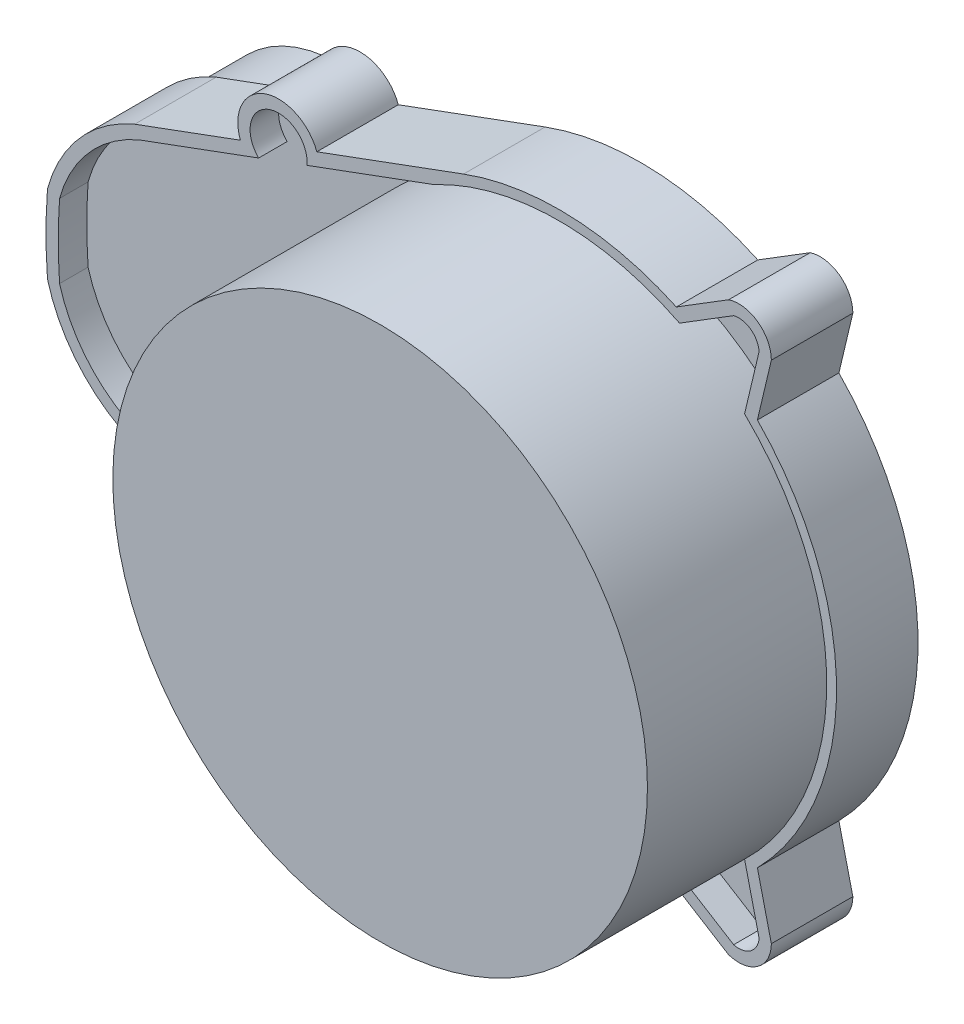
SolidWorks part; units mm, degrees
ref_plane "Plan de face" through (0, 0, 0) normal (0, 0, 1) x (1, 0, 0)
ref_plane "Plan de dessus" through (0, 0, 0) normal (0, 1, 0) x (1, 0, 0)
ref_plane "Plan de droite" through (0, 0, 0) normal (1, 0, 0) x (0, 0, -1)
sketch "Esquisse1" plane through (0, 0, 0) normal (0, 0, 1) x (1, 0, 0)
  line L0 (-11.7623, 31.9006) -> (-29.7675, 25.2618)
  line L1 (-52.1142, 17.0221) -> (-52.1142, -17.0221) construction
  line L2 (-45, 0) -> (0, 0) construction
  line L3 (-11.7623, 31.9006) -> (-11.7623, -31.9006) construction
  line L5 (-35, 25) -> (-34.4587, 23.532) construction
  line L6 (-39.15, 21.8022) -> (-52.1142, 17.0221)
  line L7 (-34.1447, 23.6478) -> (-34.7727, 23.4162)
  line L8 (20.756, 34.8016) -> (14.3413, 30.8274)
  line L9 (26, 31) -> (24.2884, 23.7923)
  line L10 (-63, 0) -> (35.5, 0) construction
  line L11 (55, 0) -> (-55, 0) construction
  line L12 (-35, -25) -> (-34.4587, -23.532) construction
  line L13 (26, -31) -> (24.2884, -23.7923)
  line L14 (20.756, -34.8016) -> (14.3413, -30.8274)
  line L15 (-34.1447, -23.6478) -> (-34.7727, -23.4162)
  line L16 (-39.15, -21.8022) -> (-52.1142, -17.0221)
  line L17 (-11.7623, -31.9006) -> (-29.7675, -25.2618)
  arc A1 (24.2884, -23.7923) -> (24.2884, 23.7923) centre (0, 0) ccw
  arc A3 (-62.8182, 4.7829) -> (-62.8182, -4.7829) centre (0, 0) ccw
  arc A4 (-52.1142, 17.0221) -> (-62.8182, 4.7829) centre (-45, 0) ccw
  circle A5 centre (22, 31) radius 1.6
  circle A6 centre (-35, 25) radius 1.6
  arc A7 (-29.7675, 25.2618) -> (-39.15, 21.8022) centre (-34.4587, 23.532) ccw
  arc A8 (26, 31) -> (20.756, 34.8016) centre (22, 31) ccw
  arc A9 (14.3413, 30.8274) -> (-11.7623, 31.9006) centre (0, 0) ccw
  arc A10 (14.3413, -30.8274) -> (-11.7623, -31.9006) centre (0, 0) cw
  arc A11 (26, -31) -> (20.756, -34.8016) centre (22, -31) cw
  arc A12 (-29.7675, -25.2618) -> (-39.15, -21.8022) centre (-34.4587, -23.532) cw
  circle A13 centre (-35, -25) radius 1.6
  circle A14 centre (22, -31) radius 1.6
  arc A15 (-52.1142, -17.0221) -> (-62.8182, -4.7829) centre (-45, 0) cw
  point P28 (-11.7623, 0)
  point P29 (-52.1142, 0)
  point P41 (34, 0)
  point P42 (-63, 0)
  dimension "D1" = 68
  dimension "D2" = 12
  dimension "D4" = 126
  dimension "D6" = 3.2
  dimension "D10" = 10
  dimension "D11" = 8
  dimension "D3" = 45
  dimension "D5" = 31
  dimension "D7" = 22
  dimension "D8" = 57
  dimension "D9" = 25
  dimension "D12" = 97
extrude "Boss.-Extru.1" add sketch "Esquisse1" along normal blind 10 contours A15 L16 A12 L17 A10 L14 A11 L13 A1 L9 A8 L8 A9 L0 A7 L6 A4 A3 A13 A5 A6 A14
sketch "Esquisse2" plane through (0, 0, 10) normal (0, 0, 1) x (1, 0, 0)
  circle A0 centre (0, 0) radius 32.8
  dimension "D1" = 65.6
extrude "Boss.-Extru.2" add sketch "Esquisse2" along normal blind 22
sketch "Esquisse3" plane through (0, 0, 10) normal (0, 0, 1) x (1, 0, 0)
  line L16 (-51.5646, -15.626) -> (-36.9068, -21.0306)
  line L17 (14.4327, -29.1195) -> (21.3751, -33.4206)
  line L18 (24.4952, -31.1553) -> (22.635, -23.3218)
  line L19 (22.635, 23.3218) -> (24.4952, 31.1553)
  line L20 (21.3751, 33.4206) -> (14.4327, 29.1195)
  line L21 (-11.2434, 30.4932) -> (-30.9728, 23.2186)
  line L22 (-51.5646, -15.626) -> (-36.9068, -21.0306)
  line L23 (14.4327, -29.1195) -> (21.3751, -33.4206)
  line L24 (24.4952, -31.1553) -> (22.635, -23.3218)
  line L25 (22.635, 23.3218) -> (24.4952, 31.1553)
  line L26 (21.3751, 33.4206) -> (14.4327, 29.1195)
  line L27 (-11.2434, 30.4932) -> (-30.9728, 23.2186)
  line L28 (-30.9728, -23.2186) -> (-11.2434, -30.4932)
  line L29 (-30.9728, -23.2186) -> (-11.2434, -30.4932)
  line L30 (-36.9068, 21.0306) -> (-51.5646, 15.626)
  line L31 (-36.9068, 21.0306) -> (-51.5646, 15.626)
  arc A20 (-61.3331, -4.5272) -> (-51.5646, -15.626) centre (-45, 0) ccw
  arc A21 (-11.2434, -30.4932) -> (14.4327, -29.1195) centre (0, 0) ccw
  arc A22 (22.635, -23.3218) -> (22.635, 23.3218) centre (0, 0) ccw
  arc A23 (14.4327, 29.1195) -> (-11.2434, 30.4932) centre (0, 0) ccw
  arc A24 (-51.5646, 15.626) -> (-61.3331, 4.5272) centre (-45, 0) ccw
  arc A25 (-61.3331, 4.5272) -> (-61.3331, -4.5272) centre (0, 0) ccw
  arc A26 (-61.3331, -4.5272) -> (-51.5646, -15.626) centre (-45, 0) ccw
  arc A27 (-11.2434, -30.4932) -> (14.4327, -29.1195) centre (0, 0) ccw
  arc A28 (22.635, -23.3218) -> (22.635, 23.3218) centre (0, 0) ccw
  arc A29 (14.4327, 29.1195) -> (-11.2434, 30.4932) centre (0, 0) ccw
  arc A30 (-51.5646, 15.626) -> (-61.3331, 4.5272) centre (-45, 0) ccw
  arc A31 (-61.3331, 4.5272) -> (-61.3331, -4.5272) centre (0, 0) ccw
  arc A32 (-36.9068, -21.0306) -> (-30.9728, -23.2186) centre (-34.4587, -23.532) ccw
  arc A33 (-36.9068, -21.0306) -> (-30.9728, -23.2186) centre (-34.4587, -23.532) ccw
  arc A34 (21.3751, -33.4206) -> (24.4952, -31.1553) centre (22, -31) ccw
  arc A35 (21.3751, -33.4206) -> (24.4952, -31.1553) centre (22, -31) ccw
  arc A36 (24.4952, 31.1553) -> (21.3751, 33.4206) centre (22, 31) ccw
  arc A37 (24.4952, 31.1553) -> (21.3751, 33.4206) centre (22, 31) ccw
  arc A38 (-30.9728, 23.2186) -> (-36.9068, 21.0306) centre (-34.4587, 23.532) ccw
  arc A39 (-30.9728, 23.2186) -> (-36.9068, 21.0306) centre (-34.4587, 23.532) ccw
  dimension "D1" = 1.5
extrude "Enlèv. mat.-Extru.1" cut sketch "Esquisse3" against normal blind 3.5
sketch "Esquisse4" plane through (0, 0, 10) normal (0, 0, -1) x (-1, 0, 0)
  line L6 (-22.7156, 23.661) -> (-22.635, 23.3218)
  line L7 (-22.7156, 23.661) -> (-22.635, 23.3218)
  line L8 (-22.635, -23.3218) -> (-22.7156, -23.661)
  line L9 (-22.635, -23.3218) -> (-22.7156, -23.661)
  line L10 (-14.7324, -29.3052) -> (-14.4327, -29.1195)
  line L11 (-14.7324, -29.3052) -> (-14.4327, -29.1195)
  line L12 (11.2434, -30.4932) -> (15.3962, -28.962)
  line L13 (11.2434, -30.4932) -> (15.3962, -28.962)
  line L14 (15.3962, 28.962) -> (11.2434, 30.4932)
  line L15 (15.3962, 28.962) -> (11.2434, 30.4932)
  line L16 (-14.4327, 29.1195) -> (-14.7324, 29.3052)
  line L17 (-14.4327, 29.1195) -> (-14.7324, 29.3052)
  arc A1 (-22.635, 23.3218) -> (-22.635, -23.3218) centre (0, 0) ccw
  arc A8 (-22.635, 23.3218) -> (-22.635, -23.3218) centre (0, 0) ccw
  arc A9 (-22.7156, -23.661) -> (-14.7324, -29.3052) centre (0, 0) ccw
  arc A10 (-22.7156, -23.661) -> (-14.7324, -29.3052) centre (0, 0) ccw
  arc A11 (-14.4327, -29.1195) -> (11.2434, -30.4932) centre (0, 0) ccw
  arc A12 (-14.4327, -29.1195) -> (11.2434, -30.4932) centre (0, 0) ccw
  arc A13 (15.3962, -28.962) -> (15.3962, 28.962) centre (0, 0) ccw
  arc A14 (15.3962, -28.962) -> (15.3962, 28.962) centre (0, 0) ccw
  arc A15 (11.2434, 30.4932) -> (-14.4327, 29.1195) centre (0, 0) ccw
  arc A16 (11.2434, 30.4932) -> (-14.4327, 29.1195) centre (0, 0) ccw
  arc A17 (-14.7324, 29.3052) -> (-22.7156, 23.661) centre (0, 0) ccw
  arc A18 (-14.7324, 29.3052) -> (-22.7156, 23.661) centre (0, 0) ccw
  dimension "D1" = 0
extrude "Boss.-Extru.3" add sketch "Esquisse4" along normal up to next
sketch "Esquisse5" plane through (0, 0, 0) normal (0, 0, -1) x (-1, 0, 0)
  circle A0 centre (47, 0) radius 16
  dimension "D2" = 32
  dimension "D1" = 47
extrude "Boss.-Extru.4" add sketch "Esquisse5" along normal blind 10
